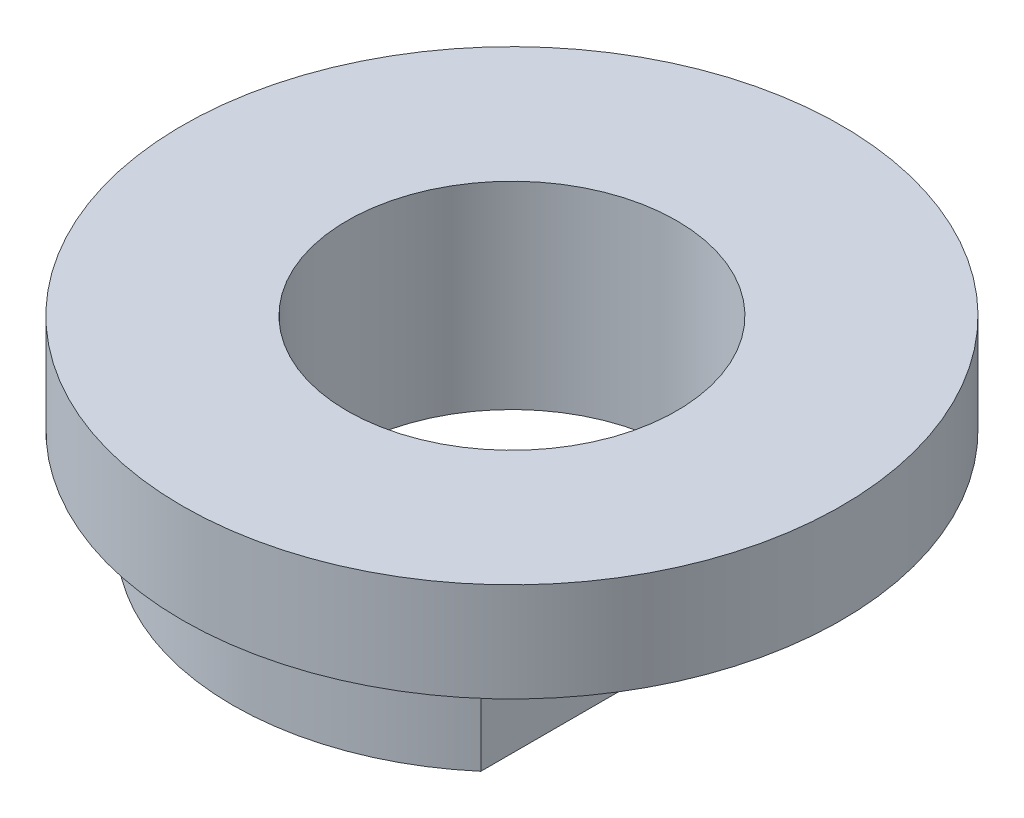
SolidWorks part; units mm, degrees
material "6063-T6"
ref_plane "Front Plane" through (0, 0, 0) normal (0, 0, 1) x (1, 0, 0)
ref_plane "Top Plane" through (0, 0, 0) normal (0, 1, 0) x (1, 0, 0)
ref_plane "Right Plane" through (0, 0, 0) normal (1, 0, 0) x (0, 0, -1)
sketch "Sketch1" plane through (0, 0, 0) normal (0, 1, 0) x (1, 0, 0)
  line L0 (-206.5127, 493.1722) -> (158.8207, 493.1722) construction
  line L1 (-281.5394, 229.2038) -> (-281.5394, 216.4038)
  line L2 (-270.5394, 229.2038) -> (-270.5394, 216.4038)
  circle A2 centre (-276.0394, 222.8469) radius 5
  arc A3 (-281.5394, 216.4038) -> (-270.5394, 216.4038) centre (-276.0394, 222.8469) ccw
  arc A4 (-281.5394, 229.2038) -> (-270.5394, 229.2038) centre (-276.0394, 222.8469) cw
  dimension "D1" = 10
  dimension "D2" = 11
  dimension "D3" = 12.8
  dimension "D4" = 12.8
extrude "Boss-Extrude1" add sketch "Sketch1" along normal blind 3
sketch "Sketch2" plane through (0, 3, 0) normal (0, 1, 0) x (1, 0, 0)
  circle A0 centre (-276.0394, 222.8469) radius 10
  circle A1 centre (-276.0394, 222.8469) radius 5
  dimension "D1" = 20
extrude "Boss-Extrude2" add sketch "Sketch2" along normal blind 3
